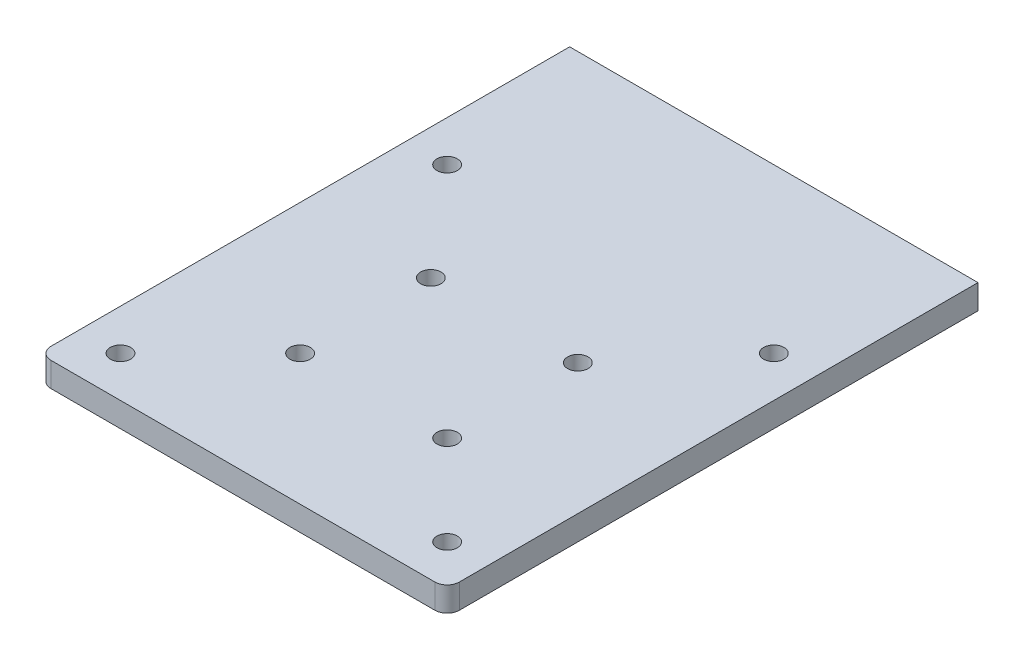
SolidWorks part; units mm, degrees
ref_plane "Front Plane" through (0, 0, 0) normal (0, 0, 1) x (1, 0, 0)
ref_plane "Top Plane" through (0, 0, 0) normal (0, 1, 0) x (1, 0, 0)
ref_plane "Right Plane" through (0, 0, 0) normal (1, 0, 0) x (0, 0, -1)
sketch "Sketch1" plane through (0, 0, 0) normal (0, 1, 0) x (1, 0, 0)
  line L1 (-10, 120) -> (90, 120)
  line L2 (-10, 120) -> (-10, -10)
  line L3 (-10, -10) -> (90, -10)
  line L4 (90, 120) -> (90, -10)
  circle A0 centre (0, 0) radius 2.5
  circle A1 centre (80, 0) radius 2.5
  circle A2 centre (0, 80) radius 2.5
  circle A3 centre (80, 80) radius 2.5
  circle A4 centre (0, 32) radius 2.5 [skipped]
  circle A5 centre (80, 32) radius 2.5 [skipped]
  circle A6 centre (22, 22) radius 2.5
  circle A7 centre (58, 22) radius 2.5
  circle A8 centre (22, 54) radius 2.5
  circle A9 centre (58, 54) radius 2.5
  dimension "D1" = 5
  dimension "D9" = 5
  dimension "D10" = 5
  dimension "D12" = 10
  dimension "D13" = 130
  dimension "D14" = 10
  dimension "D15" = 5
  dimension "D16" = 5
  dimension "D17" = 5
  dimension "D18" = 5
  dimension "D22" = 36
  dimension "D21" = 32
  dimension "D23" = 32
  dimension "D24" = 32
  dimension "D8" = 90
  dimension "D11" = 90
  dimension "D4" = 10
  dimension "D5" = 10
  dimension "D6" = 10
  dimension "D7" = 100
  dimension "D19" = 32
  dimension "D20" = 36
  dimension "D2" = 2
  dimension "D3" = 2
extrude "Boss-Extrude1" add sketch "Sketch1" along normal blind 6
fillet "Fillet1" radius 3 2 edges at (-10, 3, 10) (90, 3, 10)
